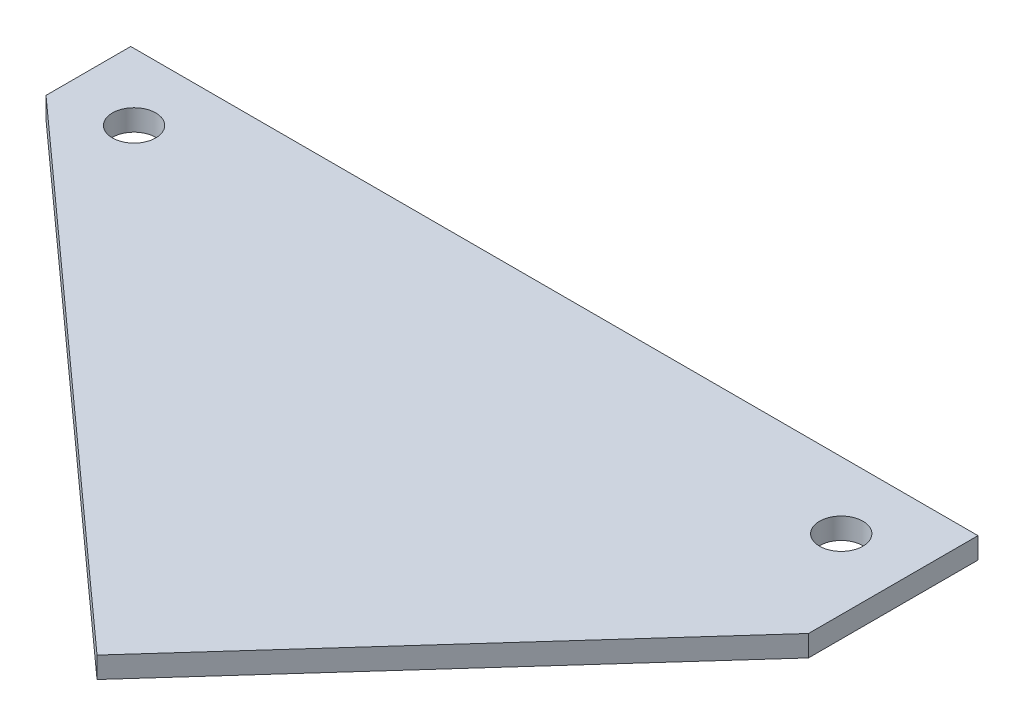
SolidWorks part; units mm, degrees
material "AISI 4130 Steel, annealed at 865C"
ref_plane "X-Y Datum" through (0, 0, 0) normal (0, 0, 1) x (1, 0, 0)
ref_plane "X-Z Datum" through (0, 0, 0) normal (0, 1, 0) x (1, 0, 0)
ref_plane "Y-Z Datum" through (0, 0, 0) normal (1, 0, 0) x (0, 0, -1)
sketch "Sketch1" plane through (0, 0, 0) normal (0, 1, 0) x (1, 0, 0)
  line L0 (0, 38.1) -> (0, -88.9)
  line L1 (-63.5, -88.9) -> (63.5, -88.9)
  line L2 (-63.5, -88.9) -> (-63.5, 38.1)
  line L3 (-63.5, 38.1) -> (63.5, 38.1)
  line L4 (63.5, -88.9) -> (63.5, 38.1)
  point P0 (0, 0)
  dimension "D1" = 127
  dimension "D2" = 38.1
  dimension "D3" = 127
extrude "Boss-Extrude1" add sketch "Sketch1" along normal blind 3.175 contours L3 L4 L1 L2
sketch "Sketch2" plane through (0, 3.175, 0) normal (0, 1, 0) x (1, 0, 0)
  line L0 (-63.5, 25.4) -> (63.5, -88.9)
  line L1 (63.5, 12.7) -> (12.9807, -43.4326)
  line L4 (-63.5, 38.1) -> (-63.5, -88.9)
  line L5 (-63.5, -88.9) -> (63.5, -88.9)
  line L6 (63.5, -88.9) -> (63.5, 38.1)
  line L7 (63.5, 38.1) -> (-63.5, 38.1)
  line L8 (-63.5, 38.1) -> (-63.5, -88.9)
  line L9 (-63.5, -88.9) -> (63.5, -88.9)
  line L10 (63.5, -88.9) -> (63.5, 38.1)
  line L11 (63.5, 38.1) -> (-63.5, 38.1)
  circle A0 centre (53, 28.1) radius 3.25 construction
  circle A1 centre (-53, 28.1) radius 3.25 construction
  circle A2 centre (53, 28.1) radius 3.25
  circle A3 centre (-53, 28.1) radius 3.25
  line M5 (-63.5, 38.1) -> (-63.5, -88.9)
  line M6 (-63.5, -88.9) -> (63.5, -88.9)
  line M7 (63.5, -88.9) -> (63.5, 38.1)
  dimension "D2" = 12.7
  dimension "D3" = 127
  dimension "D4" = 25.4
  dimension "D1" = 0
extrude "Cut-Extrude1" cut sketch "Sketch2" against normal through all contours L0 M5 M6 | A3 | A2 | L1 L0 M7 | L8 L9 L10 L11
